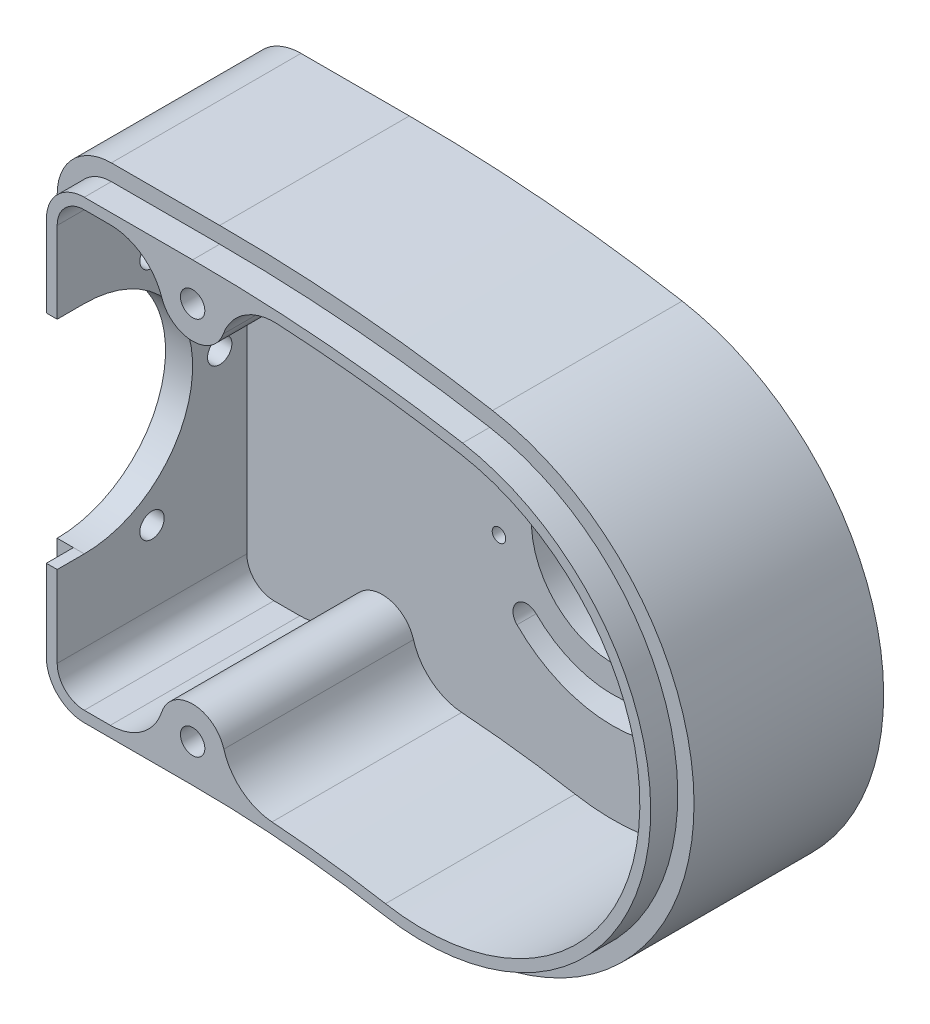
SolidWorks part; units mm, degrees
ref_plane "정면" through (0, 0, 0) normal (0, 0, 1) x (1, 0, 0)
ref_plane "윗면" through (0, 0, 0) normal (0, 1, 0) x (1, 0, 0)
ref_plane "우측면" through (0, 0, 0) normal (1, 0, 0) x (0, 0, -1)
sketch "스케치1" plane through (0, 0, 0) normal (0, 0, 1) x (1, 0, 0)
  line L0 (-1000, 0) -> (49000, 0) construction
  line L1 (0, -1000) -> (0, -44.4815) construction
  line L2 (10, -1045) -> (10, -44.4815) construction
  line L3 (0, 45.5185) -> (10, 45.5185)
  line L5 (0, -44.4815) -> (10, -44.4815)
  line L7 (0, 45.5185) -> (0, 49000) construction
  line L8 (0, 45.5185) -> (-10, 45.5185)
  line L10 (25, -44.4815) -> (-10, -44.4815)
  line L11 (-20, 35.5185) -> (-20, -34.4815)
  line L12 (10, 45.5185) -> (10, 48955) construction
  arc A1 (10, -44.4815) -> (44.7296, -47.5199) centre (10, -244.4815) cw
  arc A2 (10, 45.5185) -> (60.358, 41.1128) centre (10, -244.4815) cw
  arc A3 (-10, -44.4815) -> (-20, -34.4815) centre (-10, -34.4815) cw
  arc A4 (44.7296, -47.5199) -> (60.358, 41.1128) centre (52.5438, -3.2036) ccw
  arc A5 (-10, 45.5185) -> (-20, 35.5185) centre (-10, 35.5185) ccw
  dimension "D1" = 10
  dimension "D3" = 70
  dimension "D4" = 45
  dimension "D5" = 200
  dimension "D6" = 290
  dimension "D2" = 10
extrude "보스-돌출1" add sketch "스케치1" along normal blind 35 contours L8 A5 L11 A3 L10 L5 A1 A4 A2 L3
sketch "스케치2" plane through (0, 0, 35) normal (0, 0, 1) x (1, 0, 0)
  line L6 (10, 40.5185) -> (-10, 40.5185)
  line L7 (-15, 35.5185) -> (-15, -34.4815)
  line L8 (-10, -39.4815) -> (10, -39.4815)
  line L9 (10, 40.5185) -> (-10, 40.5185)
  line L10 (-15, 35.5185) -> (-15, -34.4815)
  line L11 (-10, -39.4815) -> (10, -39.4815)
  arc A10 (-10, 40.5185) -> (-15, 35.5185) centre (-10, 35.5185) ccw
  arc A11 (-15, -34.4815) -> (-10, -39.4815) centre (-10, -34.4815) ccw
  arc A12 (45.5979, -42.5959) -> (10, -39.4815) centre (10, -244.4815) ccw
  arc A13 (45.5979, -42.5959) -> (59.4897, 36.1887) centre (52.5438, -3.2036) ccw
  arc A14 (59.4897, 36.1887) -> (10, 40.5185) centre (10, -244.4815) ccw
  arc A15 (-10, 40.5185) -> (-15, 35.5185) centre (-10, 35.5185) ccw
  arc A16 (-15, -34.4815) -> (-10, -39.4815) centre (-10, -34.4815) ccw
  arc A17 (45.5979, -42.5959) -> (10, -39.4815) centre (10, -244.4815) ccw
  arc A18 (45.5979, -42.5959) -> (59.4897, 36.1887) centre (52.5438, -3.2036) ccw
  arc A19 (59.4897, 36.1887) -> (10, 40.5185) centre (10, -244.4815) ccw
  dimension "D1" = 5
extrude "컷-돌출1" cut sketch "스케치2" against normal blind 30
sketch "스케치3" plane through (-20, 0, 0) normal (-1, 0, 0) x (0, 0, 1)
  line L0 (35, 35.5185) -> (35, -34.4815) construction
  line L1 (22.5, 22.1692) -> (23.8748, 20.388) construction
  line L2 (22.5, -21.1321) -> (24.4937, -20.0893) construction
  line L3 (22.5, 22.1692) -> (35, 0.5185) construction
  line L4 (35, 0.5185) -> (22.5, -21.1321) construction
  circle A0 centre (35, 0.5185) radius 20
  circle A2 centre (22.5, 22.1692) radius 2.25
  circle A3 centre (10, 0.5185) radius 2.25
  circle A4 centre (22.5, -21.1321) radius 2.25
  dimension "D1" = 40
  dimension "D2" = 30
  dimension "D3" = 30
  dimension "D7" = 4.5
  dimension "D8" = 4.5
  dimension "D9" = 4.5
  dimension "D4" = 25
  dimension "D5" = 25
  dimension "D6" = 25
extrude "컷-돌출2" cut sketch "스케치3" against normal blind 10
sketch "스케치4" plane through (0, 0, 0) normal (0, 0, -1) x (-1, 0, 0)
  circle A1 centre (-52.5438, -3.2036) radius 15
  dimension "D1" = 30
extrude "컷-돌출3" cut sketch "스케치4" against normal through all both and the other way through all
sketch "스케치7" plane through (0, 0, 35) normal (0, 0, 1) x (1, 0, 0)
  line L0 (-20, 35.5185) -> (-20, -34.4815) construction
  line L1 (48, 46.2854) -> (-2, 46.2854)
  line L2 (48, 46.2854) -> (48, 25)
  line L3 (48, 25) -> (-2, 25)
  line L4 (-2, 46.2854) -> (-2, 25)
  dimension "D1" = 50
  dimension "D2" = 18
sketch "스케치8" plane through (0, 0, 35) normal (0, 0, 1) x (1, 0, 0)
  line L8 (-15, -19.4815) -> (-15, -34.4815)
  line L9 (-10, -39.4815) -> (10, -39.4815)
  line L10 (10, 40.5185) -> (-10, 40.5185)
  line L11 (-15, 35.5185) -> (-15, 20.5185)
  line L12 (-15, -19.4815) -> (-15, -34.4815)
  line L13 (-10, -39.4815) -> (10, -39.4815)
  line L14 (10, 40.5185) -> (-10, 40.5185)
  line L15 (-15, 35.5185) -> (-15, 20.5185)
  line L18 (-17, 20.5185) -> (-15, 20.5185)
  line L20 (-17, -19.4815) -> (-15, -19.4815)
  line L40 (-10, -41.4815) -> (10, -41.4815)
  line L41 (-17, -19.4815) -> (-17, -34.4815)
  line L42 (-17, 35.5185) -> (-17, 20.5185)
  line L43 (10, 42.5185) -> (-10, 42.5185)
  line L44 (-10, -41.4815) -> (10, -41.4815)
  line L45 (-17, -19.4815) -> (-17, -34.4815)
  line L46 (-17, 35.5185) -> (-17, 20.5185)
  line L47 (10, 42.5185) -> (-10, 42.5185)
  arc A10 (-15, -34.4815) -> (-10, -39.4815) centre (-10, -34.4815) ccw
  arc A11 (45.5979, -42.5959) -> (10, -39.4815) centre (10, -244.4815) ccw
  arc A12 (45.5979, -42.5959) -> (59.4897, 36.1887) centre (52.5438, -3.2036) ccw
  arc A13 (59.4897, 36.1887) -> (10, 40.5185) centre (10, -244.4815) ccw
  arc A14 (-10, 40.5185) -> (-15, 35.5185) centre (-10, 35.5185) ccw
  arc A15 (-15, -34.4815) -> (-10, -39.4815) centre (-10, -34.4815) ccw
  arc A16 (45.5979, -42.5959) -> (10, -39.4815) centre (10, -244.4815) ccw
  arc A17 (45.5979, -42.5959) -> (59.4897, 36.1887) centre (52.5438, -3.2036) ccw
  arc A18 (59.4897, 36.1887) -> (10, 40.5185) centre (10, -244.4815) ccw
  arc A19 (-10, 40.5185) -> (-15, 35.5185) centre (-10, 35.5185) ccw
  arc A41 (45.2506, -44.5655) -> (59.837, 38.1583) centre (52.5438, -3.2036) ccw
  arc A42 (45.2506, -44.5655) -> (10, -41.4815) centre (10, -244.4815) ccw
  arc A43 (-17, -34.4815) -> (-10, -41.4815) centre (-10, -34.4815) ccw
  arc A44 (-10, 42.5185) -> (-17, 35.5185) centre (-10, 35.5185) ccw
  arc A45 (59.837, 38.1583) -> (10, 42.5185) centre (10, -244.4815) ccw
  arc A46 (45.2506, -44.5655) -> (59.837, 38.1583) centre (52.5438, -3.2036) ccw
  arc A47 (45.2506, -44.5655) -> (10, -41.4815) centre (10, -244.4815) ccw
  arc A48 (-17, -34.4815) -> (-10, -41.4815) centre (-10, -34.4815) ccw
  arc A49 (-10, 42.5185) -> (-17, 35.5185) centre (-10, 35.5185) ccw
  arc A50 (59.837, 38.1583) -> (10, 42.5185) centre (10, -244.4815) ccw
  dimension "D1" = 2
  dimension "D2" = 0
extrude "보스-돌출2" add sketch "스케치8" along normal blind 5
sketch "스케치9" plane through (0, 0, 0) normal (0, 0, -1) x (-1, 0, 0)
  line L0 (-52.5438, -3.2036) -> (-52.5438, -50003.2036) construction
  line L1 (-52.5438, -3.2036) -> (49947.4562, -3.2036) construction
  line L2 (-52.5438, -3.2036) -> (35302.7953, 35352.1355) construction
  line L3 (-52.5438, -3.2036) -> (35302.7953, -35358.5426) construction
  arc A0 (-38.4017, 10.9386) -> (-34.8661, 14.4741) centre (-36.6339, 12.7063) ccw
  arc A1 (-34.8661, 14.4741) -> (-34.8661, -20.8812) centre (-52.5438, -3.2036) ccw
  arc A2 (-38.4017, 10.9386) -> (-38.4017, -17.3457) centre (-52.5438, -3.2036) ccw
  arc A3 (-34.8661, -20.8812) -> (-38.4017, -17.3457) centre (-36.6339, -19.1135) ccw
  dimension "D1" = 50
  dimension "D2" = 40
  dimension "D3" = 5
  dimension "D4" = 5
  dimension "D5" = 22.5
  dimension "D6" = 22.5
  dimension "D7" = 45
extrude "컷-돌출6" cut sketch "스케치9" against normal up to next
sketch "스케치10" plane through (0, 0, 5) normal (0, 0, 1) x (1, 0, 0)
  line L0 (52.5438, -3.2036) -> (-49947.4562, -3.2036) construction
  line L1 (52.5438, -3.2036) -> (52.5438, 49996.7964) construction
  circle A1 centre (70.0438, -3.2036) radius 1 construction
  circle A2 centre (31.5438, 1.7964) radius 1.5 construction
  circle A3 centre (31.5438, -8.2036) radius 1.5 construction
  dimension "D1" = 3
  dimension "D2" = 2
  dimension "D3" = 3
  dimension "D4" = 17.5
  dimension "D5" = 5
  dimension "D6" = 5
  dimension "D7" = 21
  dimension "D8" = 21
sketch "스케치12" plane through (0, 0, 5) normal (0, 0, 1) x (1, 0, 0)
  line L0 (0, 45.5185) -> (48438.718, 45.5185) construction
  line L1 (10, 45.5185) -> (-10, 45.5185) construction
  line L2 (1.8867, -44.4815) -> (50001.8867, -44.4815) construction
  line L4 (-20, 32.5119) -> (-20, 50032.5119) construction
  line L6 (-20, -19.4815) -> (-20, -34.4815) construction
  line L7 (10, -44.4815) -> (-10, -44.4815) construction
  circle A0 centre (10, 35.5185) radius 6
  circle A1 centre (10, -34.4815) radius 6
  point P4 (0, 45.5185)
  dimension "D1" = 12
  dimension "D4" = 12
  dimension "D2" = 10
  dimension "D3" = 30
  dimension "D5" = 10
  dimension "D6" = 30
extrude "보스-돌출3" add sketch "스케치12" along normal blind 35
fillet "필렛1" radius 10 4 edges at (13.2768, -39.5077, 22.5) (6.6834, -39.4815, 22.5) (13.346, 40.4989, 22.5) (6.6834, 40.5185, 22.5)
sketch "스케치13" plane through (0, 0, 0) normal (0, 0, -1) x (-1, 0, 0)
  line L0 (1.3375, 45.5185) -> (50001.3375, 45.5185) construction
  line L2 (3.659, -44.4815) -> (50003.659, -44.4815) construction
  line L4 (20, 11.232) -> (20, 50011.232) construction
  line L6 (-10, 45.5185) -> (10, 45.5185) construction
  line L7 (20, 35.5185) -> (20, -34.4815) construction
  line L8 (-10, -44.4815) -> (10, -44.4815) construction
  circle A0 centre (-10, 35.5185) radius 2.25
  circle A1 centre (-10, -34.4815) radius 2.25
  dimension "D1" = 4.5
  dimension "D2" = 4.5
  dimension "D3" = 10
  dimension "D4" = 30
  dimension "D5" = 10
  dimension "D6" = 30
hole_wizard "M2 나사 구멍1" positions "스케치17" profile "스케치18" tap size "M2" standard "ISO" end condition up to next
sketch "스케치17" plane through (0, 0, 5) normal (0, 0, 1) x (1, 0, 0)
  point P0 (70.0438, -3.2036)
sketch "스케치18" plane through (70.0438, -3.2036, 5) normal (1, 0, 0) x (0, -1, 0)
  line L0 (0, 0) -> (0, 5)
  line L1 (0, 5) -> (0.8, 5)
  line L2 (0.8, 5) -> (0.8, 0)
  line L5 (0.8, 0) -> (0, 0)
  line L11 (0, -6.35) -> (0, 107.95) construction
  dimension "관통 탭 드릴 지름" = 1.6
  dimension "관통 탭 드릴 깊이" = 5
cosmetic thread "구멍 나사산1" parameters "D2"=2
hole_wizard "M3 나사 구멍1" positions "스케치19" profile "스케치20" tap size "M3" standard "ISO" end condition up to next
sketch "스케치19" plane through (0, 0, 5) normal (0, 0, 1) x (1, 0, 0)
  point P0 (31.5438, 1.7964)
  point P3 (31.5438, -8.2036)
sketch "스케치20" plane through (31.5438, 1.7964, 5) normal (1, 0, 0) x (0, -1, 0)
  line L0 (0, 0) -> (0, 5)
  line L1 (0, 5) -> (1.25, 5)
  line L2 (1.25, 5) -> (1.25, 0)
  line L5 (1.25, 0) -> (0, 0)
  line L11 (0, -6.35) -> (0, 107.95) construction
  dimension "관통 탭 드릴 지름" = 2.5
  dimension "관통 탭 드릴 깊이" = 5
cosmetic thread "구멍 나사산2" parameters "D2"=3
cosmetic thread "구멍 나사산3" parameters "D2"=3
hole_wizard "M4 남비 머리 나사용 카운터보어6" positions "스케치23" profile "스케치24" counterbore size "M4" standard "ISO"
sketch "스케치23" plane through (0, 0, 0) normal (0, 0, -1) x (-1, 0, 0)
  point P0 (-10, 35.5185)
  point P3 (-10, -34.4815)
sketch "스케치24" plane through (10, 35.5185, 0) normal (1, 0, 0) x (0, 1, 0)
  line L0 (0, 0) -> (0, 41.3519)
  line L1 (0, 41.3519) -> (2.25, 40)
  line L2 (2.25, 40) -> (2.25, 33.1)
  line L3 (2.25, 33.1) -> (4.5, 33.1)
  line L4 (4.5, 33.1) -> (4.5, 0)
  line L5 (4.5, 0) -> (0, 0)
  line L10 (0, 41.3519) -> (-2.25, 40) construction
  line L11 (0, -6.35) -> (0, 107.95) construction
  dimension "구멍 지름" = 4.5
  dimension "구멍 깊이" = 40
  dimension "카운터보어 지름" = 9
  dimension "카운터보어 깊이" = 33.1
  dimension "드릴 각도" = 118
